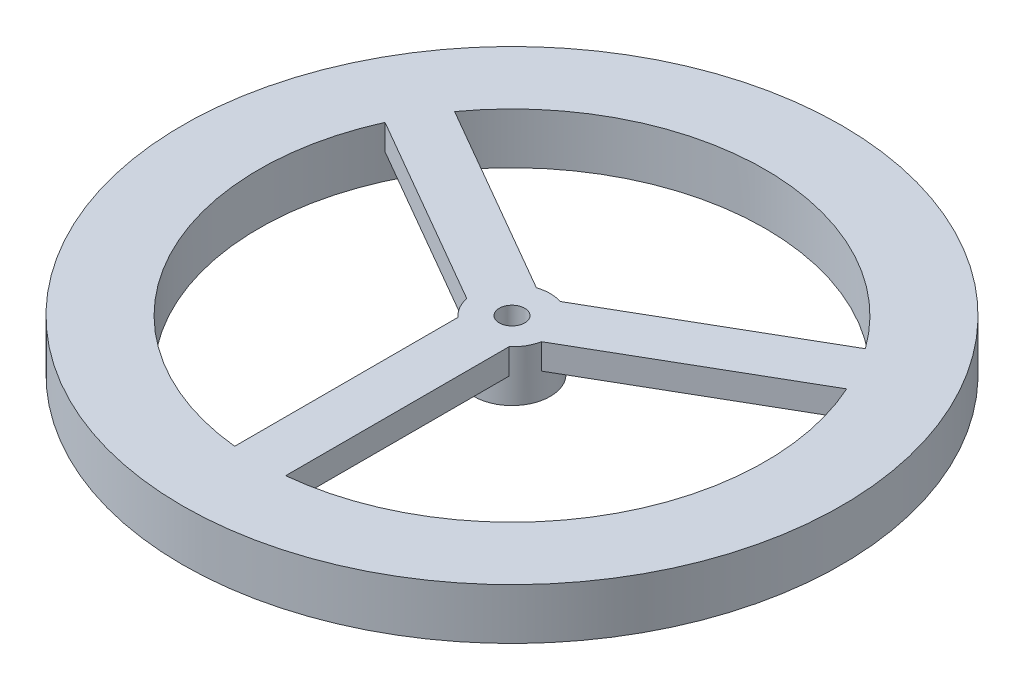
SolidWorks part; units mm, degrees
material "Pure Lead"
ref_plane "Front Plane" through (0, 0, 0) normal (0, 0, 1) x (1, 0, 0)
ref_plane "Top Plane" through (0, 0, 0) normal (0, 1, 0) x (1, 0, 0)
ref_plane "Right Plane" through (0, 0, 0) normal (1, 0, 0) x (0, 0, -1)
sketch "Sketch1" plane through (0, 0, 0) normal (0, 1, 0) x (1, 0, 0)
  circle A0 centre (0, 0) radius 64.67
  circle A1 centre (0, 0) radius 49.67
  circle A2 centre (0, 0) radius 2.5
  circle A3 centre (0, 0) radius 7.5
  dimension "D1" = 5
  dimension "D2" = 5
  dimension "D3" = 99.34
  dimension "D4" = 15
extrude "Boss-Extrude1" add sketch "Sketch1" against normal blind 10 contours A0 A1 | A3 A2
sketch "Sketch2" plane through (0, 0, 0) normal (0, 1, 0) x (1, 0, 0)
  line L0 (0, 0) -> (5, -5.5902) construction
  line L1 (-5, -5.5902) -> (5, -5.5902)
  line L2 (-5, -5.5902) -> (-5, -49.67)
  line L3 (-5, -49.67) -> (5, -49.67)
  line L4 (5, -5.5902) -> (5, -49.67)
  line L5 (0, 0) -> (5, -49.4177) construction
  line L6 (-13.4233, 0) -> (15.5933, 0) construction
  line L7 (0, 0) -> (5, 49.4177) construction
  line L8 (0, 0) -> (5, 5.5902) construction
  circle A0 centre (0, 0) radius 7.5 construction
  circle A1 centre (0, 0) radius 49.67 construction
  dimension "D1" = 10
  dimension "D2" = 96.379
  dimension "D3" = 168.445
extrude "Boss-Extrude2" add sketch "Sketch2" against normal blind 5
pattern_circular "CirPattern1" count 3 over 360 about axis through (0, 0, 0) along (0, 1, 0) of "Boss-Extrude2"
